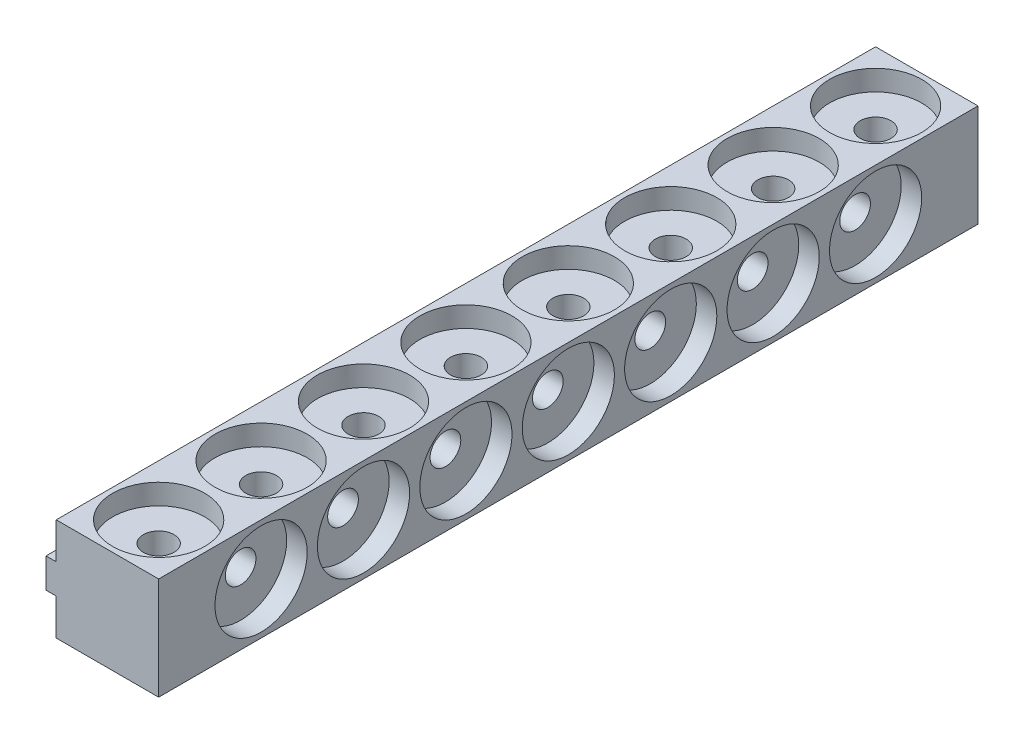
SolidWorks part; units mm, degrees
ref_plane "Front Plane" through (0, 0, 0) normal (0, 0, 1) x (1, 0, 0)
ref_plane "Top Plane" through (0, 0, 0) normal (0, 1, 0) x (1, 0, 0)
ref_plane "Right Plane" through (0, 0, 0) normal (1, 0, 0) x (0, 0, -1)
sketch "Sketch1" plane through (0, 0, 0) normal (0, 0, 1) x (1, 0, 0)
  line L0 (-10, 0) -> (-10, -3.55)
  line L1 (-10, -3.55) -> (-11, -3.55)
  line L2 (-11, -3.55) -> (-11, -6.45)
  line L3 (-11, -6.45) -> (-10, -6.45)
  line L4 (-10, -6.45) -> (-10, -10)
  line L5 (-10, -10) -> (0, -10)
  line L8 (0, -10) -> (0, 0)
  line L9 (0, 0) -> (-10, 0)
  dimension "D1" = 10
  dimension "D2" = 1
  dimension "D3" = 2.9
  dimension "D4" = 10
extrude "Boss-Extrude1" add sketch "Sketch1" along normal blind 80
sketch "Sketch2" plane through (0, 0, 0) normal (0, 1, 0) x (1, 0, 0)
  line L1 (-10, -80) -> (-10, 0) construction
  line L2 (0, -80) -> (-10, -80) construction
  circle A0 centre (-5, -75) radius 1.5
  dimension "D1" = 3
  dimension "D2" = 5
  dimension "D3" = 5
extrude "Cut-Extrude1" cut sketch "Sketch2" against normal through all
sketch "Sketch3" plane through (0, 0, 0) normal (1, 0, 0) x (0, 0, -1)
  line L0 (-80, -10) -> (-80, 0) construction
  circle A0 centre (-70, -5) radius 4.5
  dimension "D1" = 9
  dimension "D2" = 10
  dimension "D3" = 5
extrude "Cut-Extrude2" cut sketch "Sketch3" against normal blind 2
sketch "Sketch4" plane through (-2, 0, 0) normal (1, 0, 0) x (0, 0, -1)
  circle A0 centre (-70, -5) radius 1.5
  circle A1 centre (-70, -5) radius 4.5 construction
  dimension "D1" = 3
extrude "Cut-Extrude3" cut sketch "Sketch4" against normal through all
sketch "Sketch6" plane through (0, 0, 0) normal (0, 1, 0) x (1, 0, 0)
  circle A0 centre (-5, -75) radius 4.5
  circle A1 centre (-5, -75) radius 1.5 construction
  dimension "D1" = 9
extrude "Cut-Extrude4" cut sketch "Sketch6" against normal blind 2
pattern_linear "LPattern1" count 8 spacing 10 along (0, 0, -1) of "Cut-Extrude1", "Cut-Extrude4"
pattern_linear "LPattern2" count 7 spacing 10 along (0, 0, -1) of "Cut-Extrude2", "Cut-Extrude3"
